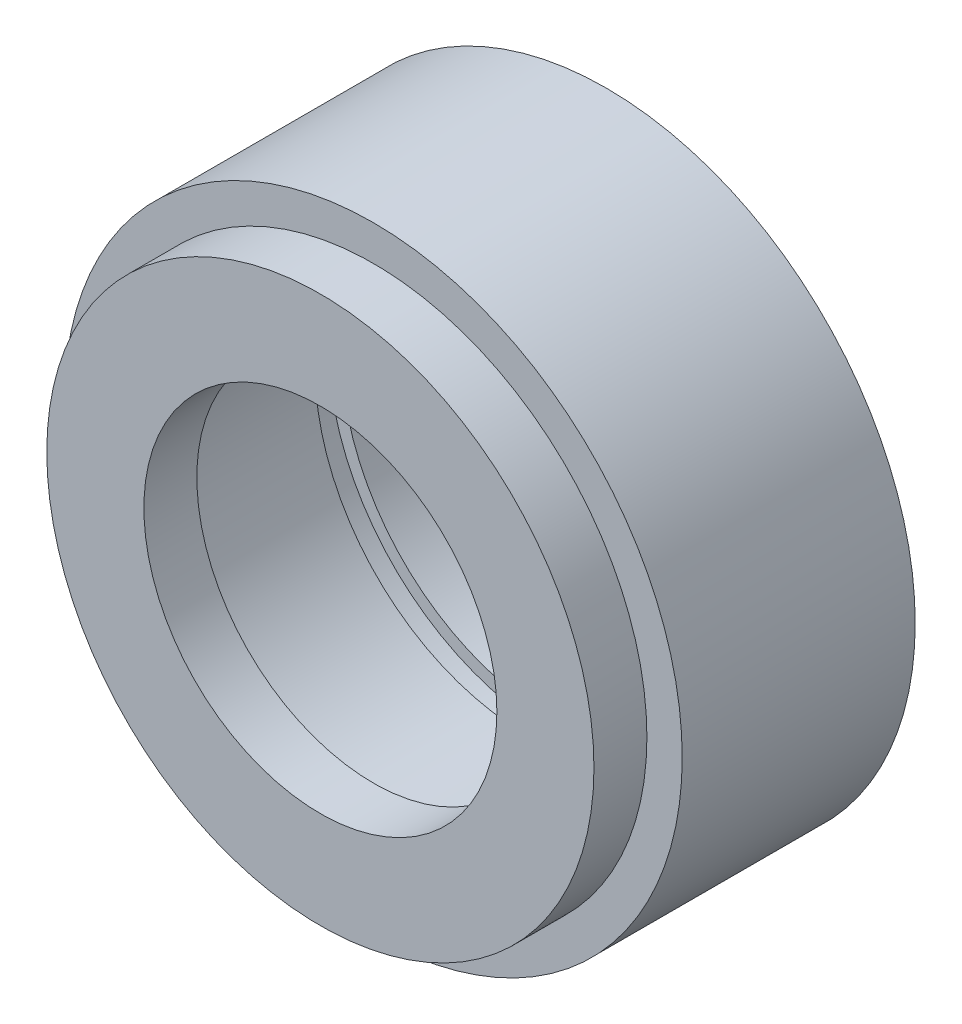
SolidWorks part; units mm, degrees
material "AISI 1020"
ref_plane "Спереди" through (0, 0, 0) normal (0, 0, 1) x (1, 0, 0)
ref_plane "Сверху" through (0, 0, 0) normal (0, 1, 0) x (1, 0, 0)
ref_plane "Справа" through (0, 0, 0) normal (1, 0, 0) x (0, 0, -1)
sketch "Эскиз1" plane through (0, 0, 0) normal (1, 0, 0) x (0, 0, -1)
  line L16 (-1000, 0) -> (49000, 0) construction
  line L17 (-9, 12) -> (-9, 10)
  line L18 (-9, 12) -> (-9, 5) construction
  line L19 (-9, 10) -> (-12, 10)
  line L20 (-12, 10) -> (-12, 15.5)
  line L21 (-12, 15.5) -> (-9, 15.5)
  line L22 (-9, 15.5) -> (-9, 17.5)
  line L23 (-9, 17.5) -> (4.2, 17.5)
  line L24 (4.2, 17.5) -> (4.2, 12)
  line L25 (4.2, 12) -> (1.2, 12)
  line L26 (1.2, 12.75) -> (1.2, -11.2161) construction
  line L27 (1.2, 12) -> (1.2, 12.75)
  line L28 (1.2, 12.75) -> (-0.3, 12.75)
  line L29 (-0.3, 12.75) -> (-0.3, 12)
  line L30 (-9, 12) -> (0, 12) construction
  line L31 (-0.3, 12) -> (-9, 12)
  dimension "D1" = 1.5
  dimension "D2" = 3
  dimension "D3" = 35
  dimension "D4" = 2
  dimension "D5" = 3
  dimension "D6" = 2
revolve "Повернуть1" add sketch "Эскиз1" angle 360 about L16
